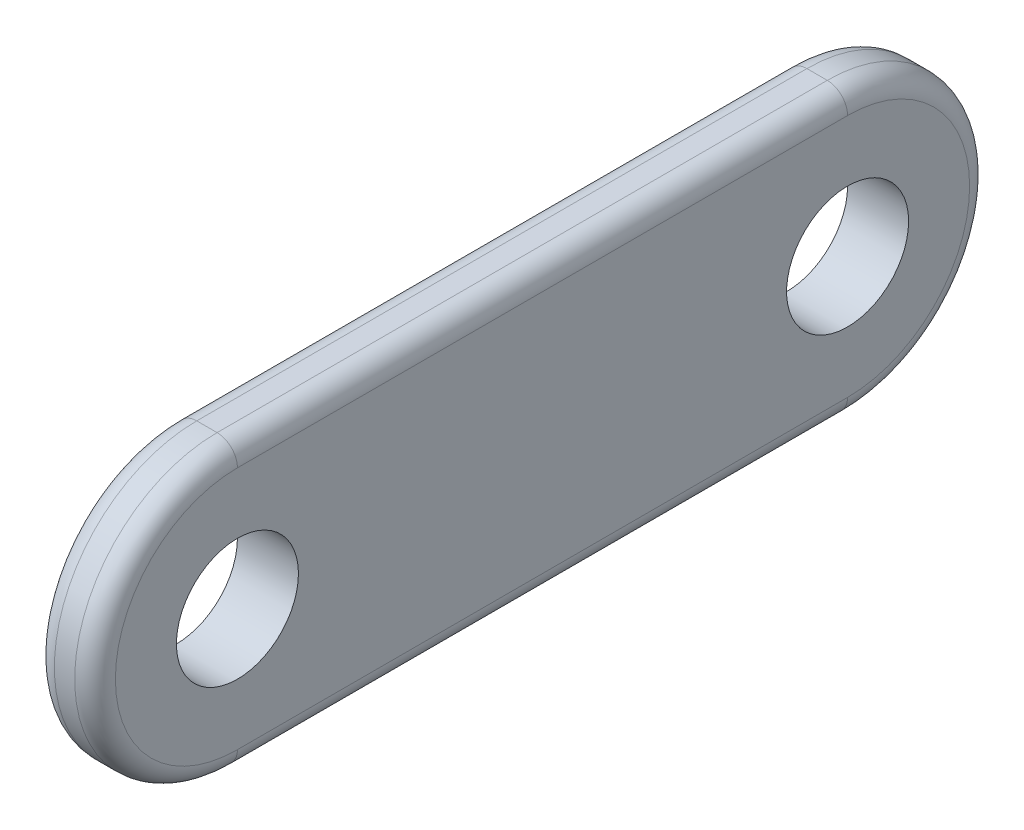
SolidWorks part; units mm, degrees
ref_plane "前视基准面" through (0, 0, 0) normal (0, 0, 1) x (1, 0, 0)
ref_plane "上视基准面" through (0, 0, 0) normal (0, 1, 0) x (1, 0, 0)
ref_plane "右视基准面" through (0, 0, 0) normal (1, 0, 0) x (0, 0, -1)
sketch "草图1" plane through (0, 0, 0) normal (1, 0, 0) x (0, 0, -1)
  line L0 (-15, 0) -> (15, 0) construction
  line L1 (-15, 7) -> (15, 7)
  line L2 (-15, -7) -> (15, -7)
  arc A0 (-15, 7) -> (-15, -7) centre (-15, 0) ccw
  arc A1 (15, -7) -> (15, 7) centre (15, 0) ccw
  circle A2 centre (-15, 0) radius 3
  circle A3 centre (15, 0) radius 3
  point P2 (0, 0)
  dimension "D2" = 7
  dimension "D3" = 6
  dimension "D1" = 30
extrude "凸台-拉伸1" add sketch "草图1" along normal blind 3
fillet "圆角1" radius 1 8 edges at (0, 0, -22) (0, -7, 0) (0, 0, 22) (3, 7, 0) (3, 0, -22) (3, -7, 0) (0, 7, 0) (3, 0, 22)
